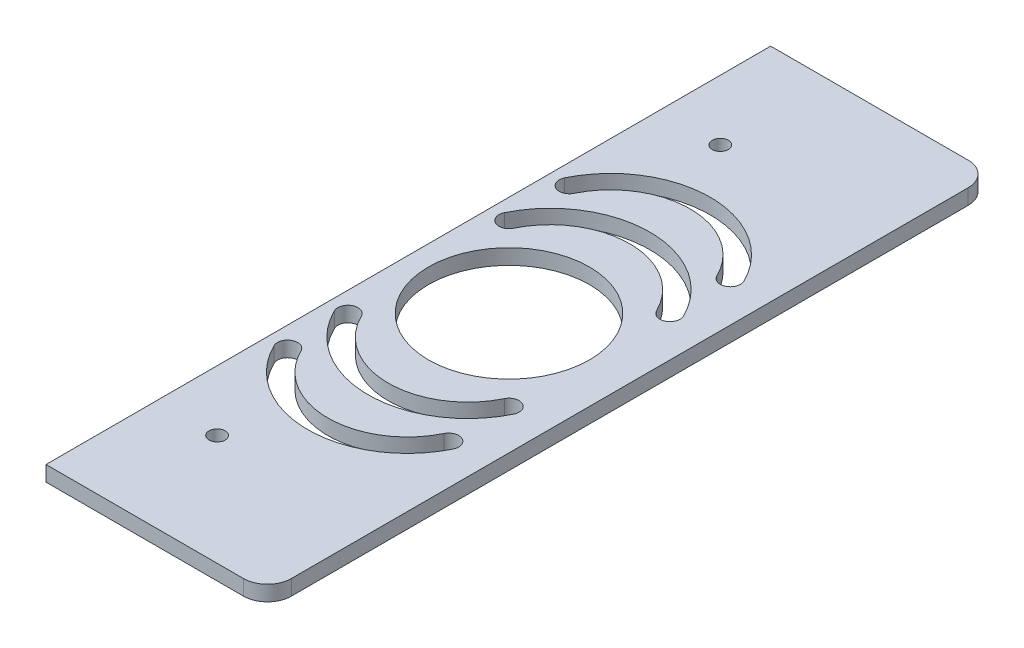
SolidWorks part; units mm, degrees
material "Acrylic (Medium-high impact)"
ref_plane "Front Plane" through (0, 0, 0) normal (0, 0, 1) x (1, 0, 0)
ref_plane "Top Plane" through (0, 0, 0) normal (0, 1, 0) x (1, 0, 0)
ref_plane "Right Plane" through (0, 0, 0) normal (1, 0, 0) x (0, 0, -1)
sketch "Sketch1" plane through (0, 0, 0) normal (0, 1, 0) x (1, 0, 0)
  line L0 (0, 0) -> (0, 457.2)
  line L1 (0, 457.2) -> (139.7, 457.2)
  line L10 (139.7, 457.2) -> (139.7, 0)
  line L11 (139.7, 0) -> (0, 0)
  circle A0 centre (63.5, 228.6) radius 50.8
  circle A1 centre (38.1, 69.85) radius 5.08
  circle A3 centre (38.1, 387.35) radius 5.08
  dimension "D11" = 10.16
  dimension "D17" = 10.16
  dimension "D3" = 101.6
  dimension "D2" = 63.5
  dimension "Length of Rib" = 457.2
  dimension "D10" = 228.6
  dimension "D12" = 69.85
  dimension "D13" = 38.1
  dimension "D18" = 38.1
  dimension "D19" = 69.85
  dimension "Width of Rib" = 139.7
extrude "Boss-Extrude1" add sketch "Sketch1" along normal blind 9.652
fillet "Fillet1" radius 15.08 2 edges at (139.7, 4.826, 0) (139.7, 4.826, -457.2)
sketch "Sketch3" plane through (0, 0, 0) normal (0, -1, 0) x (1, 0, 0)
  line L0 (63.5, -279.4) -> (63.5, -177.8) construction
  line L1 (114.3, -279.4) -> (12.7, -279.4) construction
  line L2 (114.3, -228.6) -> (114.3, -334.6005) construction
  line L3 (12.7, -228.6) -> (12.7, -334.6005) construction
  line L4 (63.5, -317.5) -> (63.5, -215.9) construction
  line L5 (114.3, -228.6) -> (12.7, -228.6) construction
  arc A0 (18.4079, -314.7174) -> (108.5921, -314.7174) centre (63.5, -292.735) ccw
  arc A1 (114.3, -279.4) -> (12.7, -279.4) centre (63.5, -254.635) cw construction
  arc A2 (6.9921, -282.1826) -> (120.0079, -282.1826) centre (63.5, -254.635) ccw
  arc A3 (18.4079, -276.6174) -> (108.5921, -276.6174) centre (63.5, -254.635) ccw
  arc A4 (18.4079, -276.6174) -> (6.9921, -282.1826) centre (12.7, -279.4) ccw
  arc A5 (120.0079, -282.1826) -> (108.5921, -276.6174) centre (114.3, -279.4) ccw
  arc A6 (18.4079, -314.7174) -> (6.9921, -320.2826) centre (12.7, -317.5) ccw
  circle A7 centre (63.5, -228.6) radius 50.8 construction
  arc A8 (120.0079, -320.2826) -> (108.5921, -314.7174) centre (114.3, -317.5) ccw
  arc A9 (6.9921, -320.2826) -> (120.0079, -320.2826) centre (63.5, -292.735) ccw
  arc A10 (114.3, -317.5) -> (12.7, -317.5) centre (63.5, -292.735) cw construction
  arc A11 (114.3, -139.7) -> (12.7, -139.7) centre (63.5, -164.465) ccw construction
  arc A12 (6.9921, -136.9174) -> (120.0079, -136.9174) centre (63.5, -164.465) cw
  arc A13 (18.4079, -142.4826) -> (108.5921, -142.4826) centre (63.5, -164.465) cw
  arc A14 (18.4079, -142.4826) -> (6.9921, -136.9174) centre (12.7, -139.7) cw
  arc A15 (120.0079, -136.9174) -> (108.5921, -142.4826) centre (114.3, -139.7) cw
  arc A16 (114.3, -177.8) -> (12.7, -177.8) centre (63.5, -202.565) ccw construction
  arc A17 (6.9921, -175.0174) -> (120.0079, -175.0174) centre (63.5, -202.565) cw
  arc A18 (18.4079, -180.5826) -> (108.5921, -180.5826) centre (63.5, -202.565) cw
  arc A19 (18.4079, -180.5826) -> (6.9921, -175.0174) centre (12.7, -177.8) cw
  arc A20 (120.0079, -175.0174) -> (108.5921, -180.5826) centre (114.3, -177.8) cw
  point P3 (63.5, -311.15)
  point P16 (63.5, -304.8)
  point P25 (63.5, -349.25)
  point P33 (63.5, -107.95)
  point P41 (63.5, -146.05)
  dimension "D2" = 12.7
  dimension "D5" = 25.4
  dimension "D1" = 25.4
  dimension "D3" = 50.8
  dimension "D4" = 2
extrude "Cut-Extrude1" cut sketch "Sketch3" against normal up to surface (9.652 mm away) up to face at (89.1477, 9.652, -228.6)
